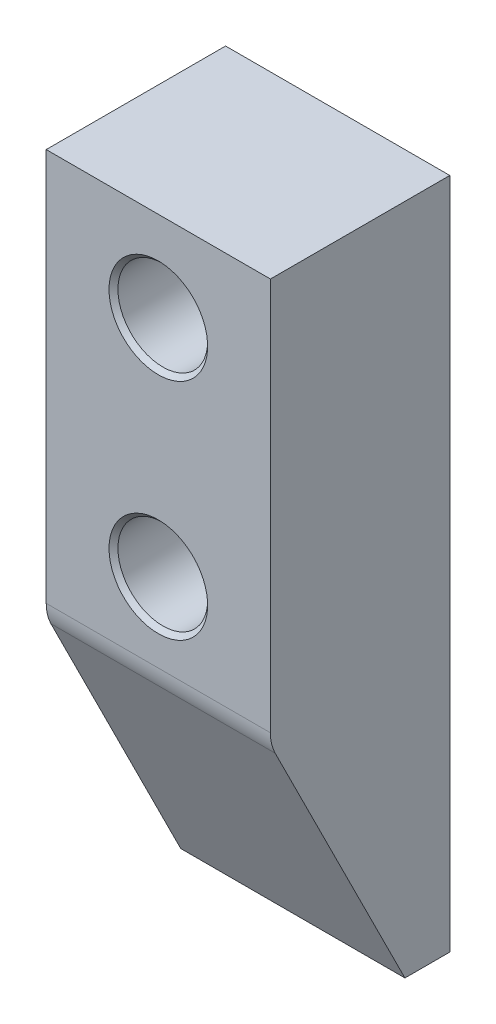
SolidWorks part; units mm, degrees
material "普通碳钢"
ref_plane "Front" through (0, 0, 0) normal (0, 0, 1) x (1, 0, 0)
ref_plane "Top" through (0, 0, 0) normal (0, 1, 0) x (1, 0, 0)
ref_plane "Right" through (0, 0, 0) normal (1, 0, 0) x (0, 0, -1)
sketch "草图1" plane through (0, 0, 0) normal (0, 0, 1) x (1, 0, 0)
  line L1 (0, 0) -> (50, 0)
  line L2 (0, 0) -> (0, 150)
  line L3 (0, 150) -> (50, 150)
  line L4 (50, 0) -> (50, 150)
  dimension "D1" = 150
  dimension "D2" = 50
extrude "凸台-拉伸1" add sketch "草图1" along normal blind 40
chamfer "倒角1" distance 30 distance2 60 1 edges at (25, 0, 40)
fillet "圆角1" radius 10 1 edges at (25, 60, 40)
sketch "草图2" plane through (0, 0, 40) normal (0, 0, 1) x (1, 0, 0)
  line L0 (25, 150) -> (25, 0) construction
  line L1 (50, 150) -> (0, 150) construction
  line L2 (50, 0) -> (0, 0) construction
  circle A0 centre (25, 130) radius 10
  circle A1 centre (25, 80) radius 10
  dimension "D1" = 20
  dimension "D3" = 20
  dimension "D4" = 20
  dimension "D2" = 50
extrude "切除-拉伸1" cut sketch "草图2" against normal blind 15
chamfer "倒角2" distance 1 angle 45 2 edges at (35, 80, 40) (35, 130, 40)
sketch "草图3" plane through (0, 0, 25) normal (0, 0, 1) x (1, 0, 0)
  circle A0 centre (25, 130) radius 5
  circle A1 centre (25, 80) radius 5
  dimension "D1" = 10
  dimension "D2" = 10
extrude "切除-拉伸2" cut sketch "草图3" against normal through all
